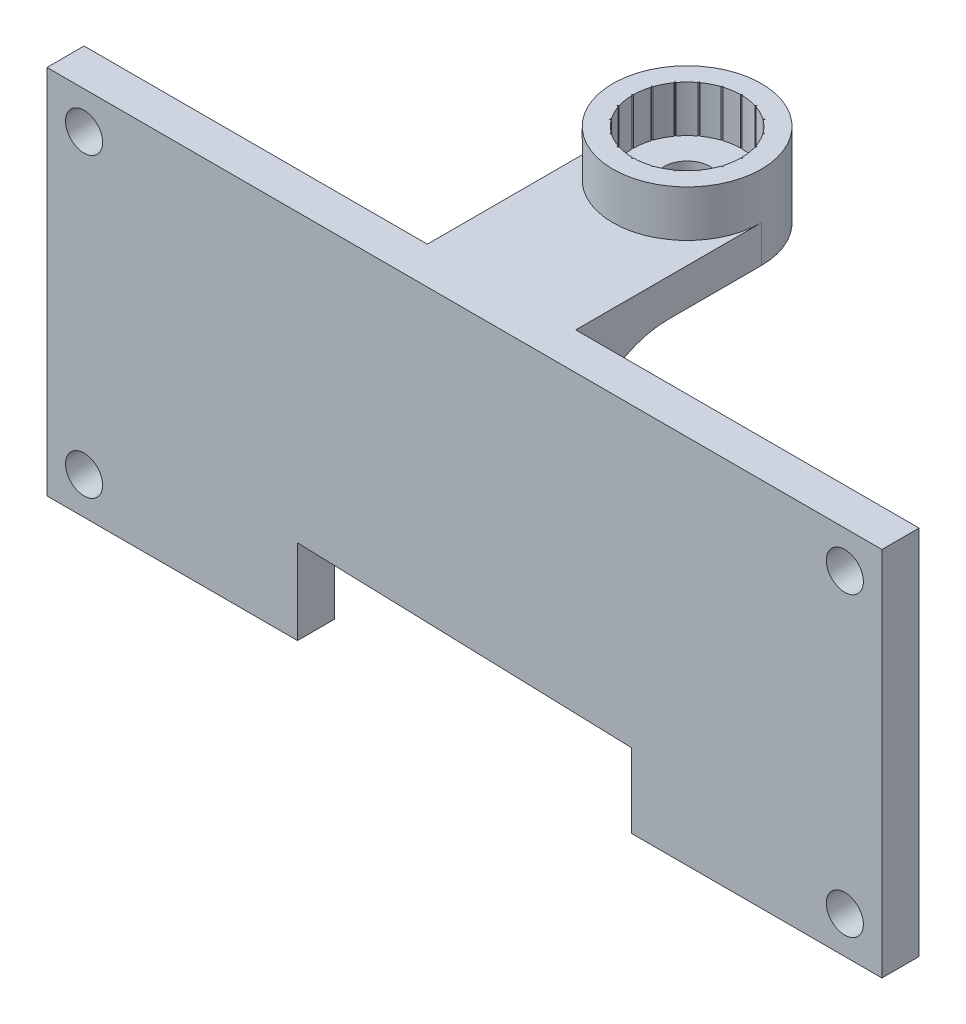
SolidWorks part; units mm, degrees
ref_plane "Front Plane" through (0, 0, 0) normal (0, 0, 1) x (1, 0, 0)
ref_plane "Top Plane" through (0, 0, 0) normal (0, 1, 0) x (1, 0, 0)
ref_plane "Right Plane" through (0, 0, 0) normal (1, 0, 0) x (0, 0, -1)
sketch "Sketch1" plane through (0, 0, 0) normal (0, 1, 0) x (1, 0, 0)
  line L0 (-36.3851, -3.3497) -> (-36.3851, -2.7252) construction
  line L1 (-36.3851, -0.3497) -> (-36.4278, -0.4235)
  line L2 (-36.3851, -0.3497) -> (-36.3425, -0.4235)
  line L3 (-35.4581, -0.4966) -> (-35.5214, -0.5536)
  line L4 (-35.4581, -0.4966) -> (-35.4404, -0.5799)
  line L5 (-34.6218, -0.9227) -> (-34.6996, -0.9574)
  line L6 (-34.6218, -0.9227) -> (-34.6307, -1.0074)
  line L7 (-33.9581, -1.5864) -> (-34.0428, -1.5953)
  line L8 (-33.9581, -1.5864) -> (-33.9928, -1.6642)
  line L9 (-33.532, -2.4227) -> (-33.6153, -2.405)
  line L10 (-33.532, -2.4227) -> (-33.589, -2.486)
  line L11 (-33.3851, -3.3497) -> (-33.4589, -3.3071)
  line L12 (-33.3851, -3.3497) -> (-33.4589, -3.3924)
  line L13 (-33.532, -4.2768) -> (-33.589, -4.2135)
  line L14 (-33.532, -4.2768) -> (-33.6153, -4.2945)
  line L15 (-33.9581, -5.1131) -> (-33.9928, -5.0352)
  line L16 (-33.9581, -5.1131) -> (-34.0428, -5.1042)
  line L17 (-34.6218, -5.7768) -> (-34.6307, -5.692)
  line L18 (-34.6218, -5.7768) -> (-34.6996, -5.7421)
  line L19 (-35.4581, -6.2029) -> (-35.4404, -6.1196)
  line L20 (-35.4581, -6.2029) -> (-35.5214, -6.1459)
  line L21 (-36.3851, -6.3497) -> (-36.3425, -6.2759)
  line L22 (-36.3851, -6.3497) -> (-36.4278, -6.2759)
  line L23 (-37.3122, -6.2029) -> (-37.2489, -6.1459)
  line L24 (-37.3122, -6.2029) -> (-37.3299, -6.1196)
  line L25 (-38.1485, -5.7768) -> (-38.0706, -5.7421)
  line L26 (-38.1485, -5.7768) -> (-38.1396, -5.692)
  line L27 (-38.8122, -5.1131) -> (-38.7274, -5.1042)
  line L28 (-38.8122, -5.1131) -> (-38.7775, -5.0352)
  line L29 (-39.2383, -4.2768) -> (-39.1549, -4.2945)
  line L30 (-39.2383, -4.2768) -> (-39.1813, -4.2135)
  line L31 (-39.3851, -3.3497) -> (-39.3113, -3.3924)
  line L32 (-39.3851, -3.3497) -> (-39.3113, -3.3071)
  line L33 (-39.2383, -2.4227) -> (-39.1813, -2.486)
  line L34 (-39.2383, -2.4227) -> (-39.1549, -2.405)
  line L35 (-38.8122, -1.5864) -> (-38.7775, -1.6642)
  line L36 (-38.8122, -1.5864) -> (-38.7274, -1.5953)
  line L37 (-38.1485, -0.9227) -> (-38.1396, -1.0074)
  line L38 (-38.1485, -0.9227) -> (-38.0706, -0.9574)
  line L39 (-37.3122, -0.4966) -> (-37.3299, -0.5799)
  line L40 (-37.3122, -0.4966) -> (-37.2489, -0.5536)
  arc A0 (-38.7775, -1.6642) -> (-39.1549, -2.405) centre (-36.3851, -3.3497) ccw
  arc A1 (-38.1396, -1.0074) -> (-38.7274, -1.5953) centre (-36.3851, -3.3497) ccw
  arc A2 (-37.3299, -0.5799) -> (-38.0706, -0.9574) centre (-36.3851, -3.3497) ccw
  arc A3 (-36.4278, -0.4235) -> (-37.2489, -0.5536) centre (-36.3851, -3.3497) ccw
  arc A4 (-35.5214, -0.5536) -> (-36.3425, -0.4235) centre (-36.3851, -3.3497) ccw
  arc A5 (-34.6996, -0.9574) -> (-35.4404, -0.5799) centre (-36.3851, -3.3497) ccw
  arc A6 (-34.0428, -1.5953) -> (-34.6307, -1.0074) centre (-36.3851, -3.3497) ccw
  arc A7 (-33.6153, -2.405) -> (-33.9928, -1.6642) centre (-36.3851, -3.3497) ccw
  arc A8 (-33.4589, -3.3071) -> (-33.589, -2.486) centre (-36.3851, -3.3497) ccw
  arc A9 (-33.589, -4.2135) -> (-33.4589, -3.3924) centre (-36.3851, -3.3497) ccw
  arc A10 (-33.9928, -5.0352) -> (-33.6153, -4.2945) centre (-36.3851, -3.3497) ccw
  arc A11 (-34.6307, -5.692) -> (-34.0428, -5.1042) centre (-36.3851, -3.3497) ccw
  arc A12 (-35.4404, -6.1196) -> (-34.6996, -5.7421) centre (-36.3851, -3.3497) ccw
  arc A13 (-36.3425, -6.2759) -> (-35.5214, -6.1459) centre (-36.3851, -3.3497) ccw
  arc A14 (-37.2489, -6.1459) -> (-36.4278, -6.2759) centre (-36.3851, -3.3497) ccw
  arc A15 (-38.0706, -5.7421) -> (-37.3299, -6.1196) centre (-36.3851, -3.3497) ccw
  arc A16 (-38.7274, -5.1042) -> (-38.1396, -5.692) centre (-36.3851, -3.3497) ccw
  arc A17 (-39.1549, -4.2945) -> (-38.7775, -5.0352) centre (-36.3851, -3.3497) ccw
  arc A18 (-39.3113, -3.3924) -> (-39.1813, -4.2135) centre (-36.3851, -3.3497) ccw
  arc A19 (-39.1813, -2.486) -> (-39.3113, -3.3071) centre (-36.3851, -3.3497) ccw
  circle A20 centre (-36.3851, -3.3497) radius 4
  point P1 (0, 0)
  point P64 (-36.3851, -3.3497)
  dimension "D3" = 8
  dimension "D1" = 30
extrude "Boss-Extrude1" add sketch "Sketch1" along normal blind 2.5 contours L0 A20 L2 A4 L3 L4 A5 L5 L6 A6 L7 L8 A7 L9 L10 A8 L11 L12 A9 L13 L14 A10 L15 L16 A11 L17 L18 A12 L19 L20 A13 L21 | A20 L0 L22 A14 L23 L24 A15 L25 L26 A16 L27 L28 A17 L29 L30 A18 L31 L32 A19 L33 L34 A0 L35 L36 A1 L37 L38 A2 L39 L40 A3 L1
sketch "Sketch2" plane through (0, 0, 0) normal (0, -1, 0) x (1, 0, 0)
  line L0 (-40.3851, -0.6503) -> (-32.3851, -0.6503)
  line L1 (-32.3851, -6.6503) -> (-40.3851, -6.6503)
  line L2 (-32.3851, -6.6503) -> (-32.3851, 13.3497)
  line L3 (-32.3851, 13.3497) -> (-40.3851, 13.3497)
  line L4 (-40.3851, -6.6503) -> (-40.3851, 13.3497)
  line L5 (-32.3851, -6.6503) -> (-40.3851, 13.3497) construction
  line L6 (-32.3851, 13.3497) -> (-40.3851, -6.6503) construction
  circle A0 centre (-36.3851, 3.3497) radius 4 construction
  circle A1 centre (-36.3851, 3.3497) radius 4
  point P7 (-36.3851, -0.6503)
extrude "Boss-Extrude5" add sketch "Sketch2" along normal blind 2 contours L0 A1 L2 L3 L4 | A1
sketch "Sketch10" plane through (0, 0, 13.3497) normal (0, 0, 1) x (1, 0, 0)
  line L0 (-58.8851, 0) -> (-13.8851, 0)
  line L1 (-58.8851, -20) -> (-13.8851, -20)
  line L2 (-58.8851, 0) -> (-58.8851, -20)
  line L3 (-13.8851, -20) -> (-13.8851, 0)
  line L4 (-32.3851, -2) -> (-40.3851, -2) construction
  line L5 (-32.3851, 0) -> (-40.3851, 0) construction
  line L6 (-27.3895, -20) -> (-27.3895, -16)
  line L7 (-27.3895, -16) -> (-45.3808, -15.4394)
  line L8 (-45.3808, -15.4394) -> (-45.3808, -20)
  circle A0 centre (-15.8851, -18) radius 1
  circle A1 centre (-15.8851, -2) radius 1
  circle A2 centre (-56.8851, -18) radius 1
  circle A3 centre (-56.8851, -2) radius 1
  point P3 (-36.3851, 0)
  point P5 (-36.3851, -2)
  point P6 (-36.3851, -20)
  point P7 (-36.3851, 0)
  point P14 (-36.3851, -15.7197)
  point P17 (-15.8851, -18)
  point P18 (-56.8851, -18)
  point P19 (-56.8851, -2)
  point P20 (-15.8851, -2)
  point P29 (-14.8851, -2)
  point P30 (-15.8851, -1)
  line M3 (-32.3851, 0) -> (-40.3851, 0)
  line M4 (-40.3851, 0) -> (-40.3851, -2)
  line M5 (-40.3851, -2) -> (-32.3851, -2)
  line M6 (-32.3851, -2) -> (-32.3851, 0)
  dimension "D11" = 1
  dimension "D10" = 2
  dimension "D1" = 20
  dimension "D2" = 45
  dimension "D3" = 2
  dimension "D4" = 2
  dimension "D5" = 2
  dimension "D6" = 2
  dimension "D7" = 2
  dimension "D8" = 2
  dimension "D9" = 2
extrude "Boss-Extrude6" add sketch "Sketch10" along normal blind 2 contours L8 L7 L6 L1 L3 L0 L2 M6 M5 M4 | M6 M3 M4 M5
fillet "Fillet1" radius 5 1 edges at (-36.3851, -2, 13.3497)
sketch "Sketch11" plane through (0, -2, 0) normal (0, -1, 0) x (1, 0, 0)
  circle A0 centre (-36.3851, 3.3497) radius 1.25
  point P0 (-36.3851, 3.3497)
extrude "Cut-Extrude1" cut sketch "Sketch11" against normal blind 12
